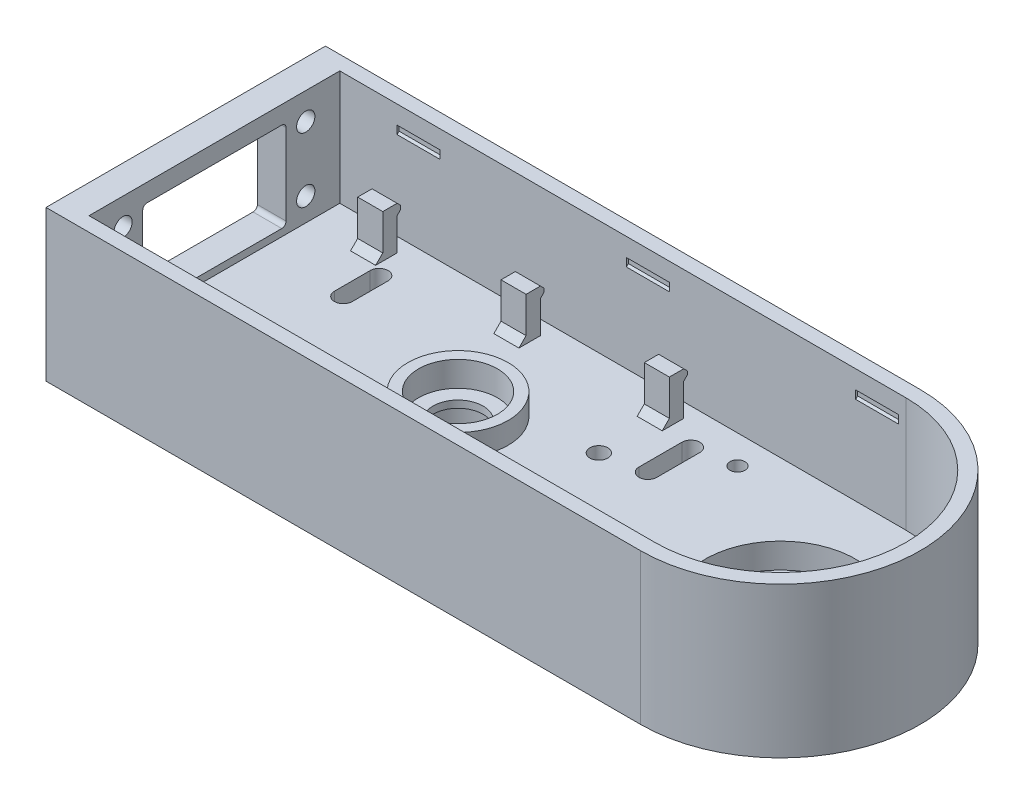
SolidWorks part; units mm, degrees
ref_plane "Front Plane" through (0, 0, 0) normal (0, 0, 1) x (1, 0, 0)
ref_plane "Top Plane" through (0, 0, 0) normal (0, 1, 0) x (1, 0, 0)
ref_plane "Right Plane" through (0, 0, 0) normal (1, 0, 0) x (0, 0, -1)
sketch "Sketch1" plane through (0, 0, 0) normal (0, 1, 0) x (1, 0, 0)
  line L0 (0, 39) -> (-166, 39)
  line L1 (-166, 39) -> (-166, -39)
  line L2 (-166, -39) -> (0, -39)
  arc A1 (0, 39) -> (0, -39) centre (0, 0) cw
  dimension "D2" = 166
extrude "Boss-Extrude1" add sketch "Sketch1" along normal blind 10
sketch "Sketch2" plane through (0, 10, 0) normal (0, 1, 0) x (1, 0, 0)
  line L0 (0, 35) -> (-158, 35)
  line L2 (-158, -35) -> (0, -35)
  line L3 (0, 39) -> (-166, 39)
  line L4 (-166, 39) -> (-166, -39)
  line L5 (-166, -39) -> (0, -39)
  line L6 (0, 39) -> (-166, 39)
  line L7 (-166, 39) -> (-166, -39)
  line L8 (-166, -39) -> (0, -39)
  line L9 (-158, 35) -> (-158, -35)
  line L10 (0, 35) -> (-162, 35) construction
  line L11 (-162, -35) -> (0, -35) construction
  line L13 (-162, 35) -> (-162, -35) construction
  arc A0 (0, -35) -> (0, 35) centre (0, 0) ccw
  arc A3 (0, -39) -> (0, 39) centre (0, 0) ccw construction
  arc A4 (0, -39) -> (0, 39) centre (0, 0) ccw
  arc A5 (0, -39) -> (0, 39) centre (0, 0) ccw
  dimension "D3" = 8
  dimension "D1" = 0
  dimension "D2" = 4
extrude "Boss-Extrude2" add sketch "Sketch2" along normal blind 32 contours L0 L9 L2 A0
sketch "Sketch3" plane through (-166, 0, 0) normal (-1, 0, 0) x (0, 0, 1)
  line L0 (-39, 0) -> (39, 0) construction
  line L1 (-20, 12) -> (20, 12)
  line L2 (-20, 12) -> (-20, 37)
  line L3 (-20, 37) -> (20, 37)
  line L4 (20, 12) -> (20, 37)
  line L5 (-20, 12) -> (20, 37) construction
  line L6 (-20, 37) -> (20, 12) construction
  circle A0 centre (-25.5, 34.5) radius 2.55
  circle A1 centre (-25.5, 16.5) radius 2.55
  circle A2 centre (25.5, 16.5) radius 2.55
  circle A3 centre (25.5, 34.5) radius 2.55
  point P0 (0, 24.5)
  dimension "D5" = 5.1
  dimension "D6" = 5.1
  dimension "D7" = 5.1
  dimension "D8" = 5.1
  dimension "D1" = 25
  dimension "D2" = 40
  dimension "D3" = 12
  dimension "D4" = 16.5
  dimension "D9" = 5.5
  dimension "D10" = 5.5
  dimension "D11" = 18
extrude "Cut-Extrude1" cut sketch "Sketch3" against normal up to next
fillet "Fillet1" radius 1.2 4 edges at (-162, 37, 20) (-162, 12, 20) (-162, 37, -20) (-162, 12, -20)
sketch "Sketch4" plane through (0, 10, 0) normal (0, 1, 0) x (1, 0, 0)
  line L0 (-91.7844, 7.0785) -> (-7.1622, 28.4111) construction
  line L1 (-91.7844, -7.0785) -> (-7.1622, -28.4111) construction
  line L2 (-90, 0) -> (0, 0) construction
  line L3 (-90, 0) -> (-238, 0) construction
  line L4 (-238.8216, 6.2966) -> (-93.2995, 25.2856) construction
  line L5 (-238.8216, -6.2966) -> (-93.2995, -25.2856) construction
  arc A0 (-7.1622, -28.4111) -> (-7.1622, 28.4111) centre (0, 0) ccw construction
  arc A1 (-91.7844, 7.0785) -> (-91.7844, -7.0785) centre (-90, 0) ccw construction
  circle A2 centre (-90, 0) radius 7
  circle A3 centre (0, 0) radius 17.5
  arc A4 (-238.8216, 6.2966) -> (-238.8216, -6.2966) centre (-238, 0) ccw construction
  arc A5 (-93.2995, -25.2856) -> (-93.2995, 25.2856) centre (-90, 0) ccw construction
  dimension "D1" = 58.6
  dimension "D2" = 14.6
  dimension "D4" = 35
  dimension "D5" = 14
  dimension "D7" = 51
  dimension "D8" = 12.7
  dimension "D3" = 90
  dimension "D6" = 148
extrude "Cut-Extrude2" cut sketch "Sketch4" against normal through all
sketch "Sketch5" plane through (0, 10, 0) normal (0, 1, 0) x (1, 0, 0)
  circle A0 centre (0, 0) radius 21
  dimension "D1" = 42
extrude "Cut-Extrude3" cut sketch "Sketch5" against normal blind 7
sketch "Sketch6" plane through (0, 10, 0) normal (0, 1, 0) x (1, 0, 0)
  circle A0 centre (-90, 0) radius 11
  circle A1 centre (-90, 0) radius 14
  dimension "D1" = 22
  dimension "D2" = 3
extrude "Boss-Extrude3" add sketch "Sketch6" along normal blind 6
sketch "Sketch7" plane through (0, 10, 0) normal (0, 1, 0) x (1, 0, 0)
  line L0 (-135, 23) -> (-135, 13) construction
  line L1 (-132.5, 23) -> (-132.5, 13)
  line L2 (-137.5, 23) -> (-137.5, 13)
  line L3 (-135, -13) -> (-135, -23) construction
  line L4 (-132.5, -13) -> (-132.5, -23)
  line L5 (-137.5, -13) -> (-137.5, -23)
  line L6 (-158, 35) -> (-158, -35) construction
  line L7 (0, 35) -> (-158, 35) construction
  line L8 (-158, -35) -> (0, -35) construction
  line L9 (-50, 25) -> (-50, 13) construction
  line L10 (-47.5, 25) -> (-47.5, 13)
  line L11 (-52.5, 25) -> (-52.5, 13)
  line L12 (0, 35) -> (-158, 35) construction
  line L13 (-50, -21) -> (-50, -25) construction
  line L14 (-47.5, -21) -> (-47.5, -25)
  line L15 (-52.5, -21) -> (-52.5, -25)
  arc A0 (-132.5, 23) -> (-137.5, 23) centre (-135, 23) ccw
  arc A1 (-137.5, 13) -> (-132.5, 13) centre (-135, 13) ccw
  arc A2 (-132.5, -13) -> (-137.5, -13) centre (-135, -13) ccw
  arc A3 (-137.5, -23) -> (-132.5, -23) centre (-135, -23) ccw
  arc A4 (-47.5, 25) -> (-52.5, 25) centre (-50, 25) ccw
  arc A5 (-52.5, 13) -> (-47.5, 13) centre (-50, 13) ccw
  arc A6 (-47.5, -21) -> (-52.5, -21) centre (-50, -21) ccw
  arc A7 (-52.5, -25) -> (-47.5, -25) centre (-50, -25) ccw
  point P2 (-135, 18)
  point P7 (-135, -18)
  point P22 (-50, 19)
  point P31 (-50, -23)
  dimension "D1" = 2.5
  dimension "D2" = 2.5
  dimension "D9" = 2.5
  dimension "D12" = 2.5
  dimension "D3" = 23
  dimension "D4" = 10
  dimension "D5" = 12
  dimension "D6" = 12
  dimension "D7" = 10
  dimension "D8" = 108
  dimension "D10" = 10
  dimension "D11" = 12
  dimension "D13" = 4
  dimension "D14" = 10
extrude "Cut-Extrude4" cut sketch "Sketch7" against normal through all
sketch "Sketch8" plane through (0, 0, 0) normal (0, -1, 0) x (1, 0, 0)
  circle A0 centre (-90, 0) radius 11
  dimension "D1" = 22
extrude "Cut-Extrude5" cut sketch "Sketch8" against normal blind 7
sketch "Sketch9" plane through (0, 10, 0) normal (0, 1, 0) x (1, 0, 0)
  line L0 (0, 35) -> (-158, 35) construction
  line L1 (-158, 35) -> (-158, -35) construction
  line L2 (-158, -35) -> (0, -35) construction
  line L3 (-58, -9.46) -> (-49.612, -5) construction
  line L4 (-158, -35) -> (0, -35) construction
  circle A0 centre (-39, 27) radius 2.1
  arc A1 (-47.5, 25) -> (-52.5, 25) centre (-50, 25) ccw construction
  circle A2 centre (-61.5, 10.8097) radius 2.5
  arc A3 (-52.5, 13) -> (-47.5, 13) centre (-50, 13) ccw construction
  circle A4 centre (-58, -9.46) radius 1.6
  circle A5 centre (-49.612, -5) radius 1.6
  dimension "D1" = 8
  dimension "D2" = 11
  dimension "D3" = 4.2
  dimension "D6" = 5
  dimension "D9" = 3.2
  dimension "D10" = 3.2
  dimension "D4" = 24.1903
  dimension "D5" = 11.5
  dimension "D7" = 100
  dimension "D8" = 9.5
  dimension "D11" = 30
  dimension "D12" = 28
extrude "Cut-Extrude6" cut sketch "Sketch9" against normal through all
ref_plane "Plane1" through (-145, 0, 0) normal (1, 0, 0) x (0, 0, -1)
sketch "Sketch10" plane through (-145, 0, 0) normal (1, 0, 0) x (0, 0, -1)
  line L0 (31, 10) -> (31, 19)
  line L1 (35, 10) -> (-35, 10) construction
  line L2 (31, 19) -> (32, 20)
  line L3 (32, 20) -> (32, 21)
  line L4 (32, 21) -> (31, 22)
  line L5 (31, 22) -> (27, 22)
  line L6 (27, 22) -> (27, 10)
  line L8 (35, 10) -> (-35, 10)
  line L9 (35, 42) -> (35, 10) construction
  dimension "D1" = 4
  dimension "D2" = 4
  dimension "D3" = 3
  dimension "D4" = 4
  dimension "D5" = 135
  dimension "D6" = 135
  dimension "D7" = 1
  dimension "D8" = 12
extrude "Boss-Extrude4" add sketch "Sketch10" along normal blind 7 contours L8 L0 L2 L3 L4 L5 L6
chamfer "Chamfer1" distance 2 angle 45 1 edges at (-141.5, 10, -27)
pattern_linear "LPattern1" count 3 spacing 40 along (1, 0, 0) of "Boss-Extrude4", "Chamfer1"
ref_plane "Plane2" through (-142, 0, 0) normal (-1, 0, 0) x (0, 0, 1)
sketch "Sketch11" plane through (-142, 0, 0) normal (-1, 0, 0) x (0, 0, 1)
  line L7 (-35, 42) -> (-35, 10) construction
  line L8 (-35, 42) -> (-35, 10)
  line L19 (-35, 42) -> (35, 42) construction
  line L20 (-35, 42) -> (35, 42)
  line L21 (-34.4, 42) -> (-34.4, 37.5)
  line L22 (-34.4, 37.5) -> (-35.55, 36.35)
  line L23 (-35.55, 36.35) -> (-35.55, 35.15)
  line L24 (-35.55, 35.15) -> (-34.4, 34)
  line L25 (-34.4, 34) -> (-30.9, 34)
  line L26 (-30.9, 34) -> (-30.9, 42)
  line L27 (-39, 42) -> (-39, 0) construction
  dimension "D7" = 3.5
  dimension "D8" = 3.5
  dimension "D9" = 1.2
  dimension "D10" = 135
  dimension "D11" = 135
  dimension "D12" = 8
  dimension "D13" = 4.5
  dimension "D14" = 4.6
extrude "Cut-Extrude7" cut sketch "Sketch11" against normal blind 12 contours L23 L24 L8 L22
pattern_linear "LPattern2" count 3 spacing 64 along (1, 0, 0) of "Cut-Extrude7"
mirror "Mirror1" about plane through (0, 0, 0) normal (0, 0, 1) of "LPattern2", "Cut-Extrude7"
sketch "Sketch12" plane through (0, 0, 0) normal (0, 0, 1) x (1, 0, 0)
  line L0 (39, 42) -> (0, 42) construction
  line L1 (39, 42) -> (0, 42)
  line L2 (34.4, 42) -> (34.4, 37.5)
  line L3 (34.4, 37.5) -> (35.55, 36.35)
  line L4 (35.55, 36.35) -> (35.55, 35.15)
  line L5 (35.55, 35.15) -> (34.4, 34)
  line L6 (34.4, 34) -> (30.9, 34)
  line L7 (30.9, 34) -> (30.9, 42)
  line L8 (35, 42) -> (35, 32.2725)
  line L9 (0, 42) -> (0, 38.3259)
  dimension "D1" = 3.5
  dimension "D2" = 3.5
  dimension "D3" = 8
  dimension "D4" = 135
  dimension "D5" = 1.2
  dimension "D6" = 4.5
  dimension "D7" = 4.6
  dimension "D8" = 4
revolve "Cut-Revolve1" cut sketch "Sketch12" angle 20 mid plane about L9
sketch "Sketch13" plane through (0, 10, 0) normal (0, 1, 0) x (1, 0, 0)
  circle A1 centre (-90, 0) radius 11
  circle A2 centre (-90, 0) radius 11
  dimension "D1" = 0
extrude "Cut-Extrude8" cut sketch "Sketch13" against normal blind 1
